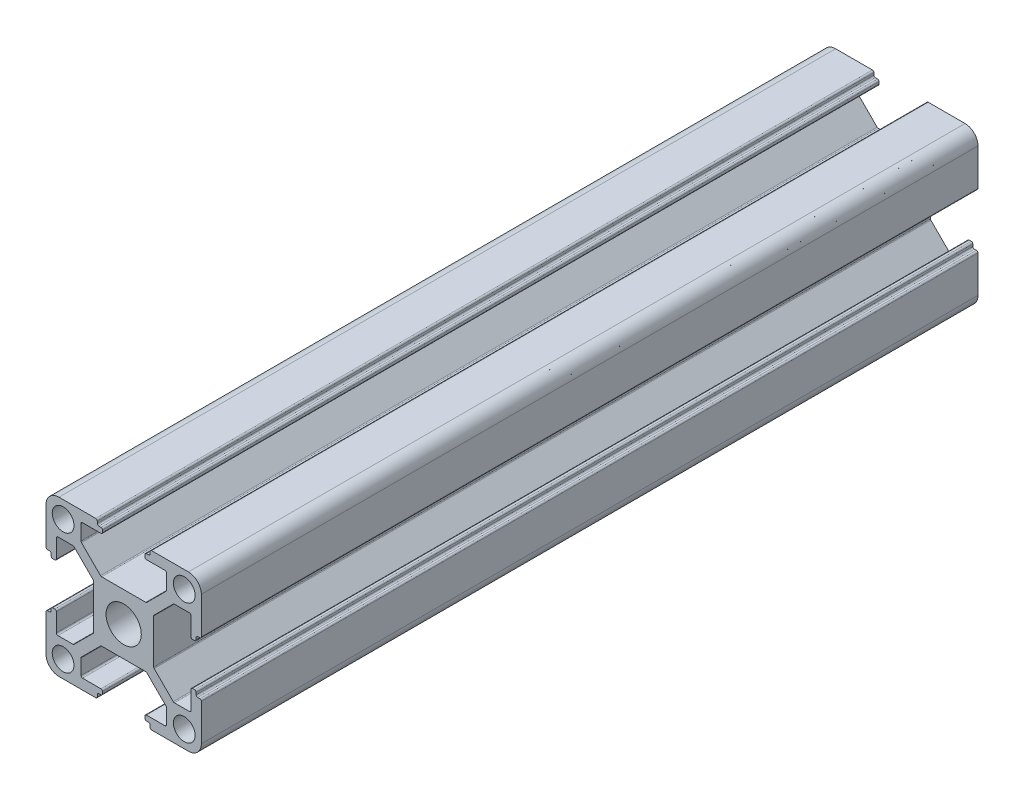
SolidWorks part; units mm, degrees
ref_plane "Alzado" through (0, 0, 0) normal (0, 0, 1) x (1, 0, 0)
ref_plane "Planta" through (0, 0, 0) normal (0, 1, 0) x (1, 0, 0)
ref_plane "Vista lateral" through (0, 0, 0) normal (1, 0, 0) x (0, 0, -1)
ref_plane "Plano1" through (0, 0, -50) normal (0, 0, -1) x (-1, 0, 0)
sketch "Croquis1" plane through (0, 0, -50) normal (0, 0, -1) x (-1, 0, 0)
  line L0 (14.7, -5.1) -> (14.3, -5.1)
  line L1 (14, -4.8) -> (14, -4.4)
  line L2 (13.7, -4.1) -> (13.3, -4.1)
  line L3 (13, -4.4) -> (13, -7.95)
  line L4 (12.7, -8.25) -> (9.7893, -8.25)
  line L5 (9.5772, -8.1622) -> (5.8879, -4.4739)
  line L6 (5.8, -4.2617) -> (5.8, 4.2607)
  line L7 (5.8879, 4.4729) -> (9.5771, 8.1621)
  line L8 (9.7893, 8.25) -> (12.7, 8.25)
  line L9 (13, 7.95) -> (13, 4.4)
  line L10 (13.3, 4.1) -> (13.7, 4.1)
  line L11 (14, 4.4) -> (14, 4.8)
  line L12 (14.3, 5.1) -> (14.7, 5.1)
  line L13 (15, 5.4) -> (15, 12.5)
  line L14 (12.5, 15) -> (5.4, 15)
  line L15 (5.1, 14.7) -> (5.1, 14.3)
  line L16 (4.8, 14) -> (4.4, 14)
  line L17 (4.1, 13.7) -> (4.1, 13.3)
  line L18 (4.4, 13) -> (7.95, 13)
  line L19 (8.25, 12.7) -> (8.25, 9.7883)
  line L20 (8.1621, 9.5761) -> (4.4739, 5.8879)
  line L21 (4.2617, 5.8) -> (-4.2607, 5.8)
  line L22 (-4.4728, 5.8878) -> (-8.1621, 9.5761)
  line L23 (-8.25, 9.7883) -> (-8.25, 12.7)
  line L24 (-7.95, 13) -> (-4.4, 13)
  line L25 (-4.1, 13.3) -> (-4.1, 13.7)
  line L26 (-4.4, 14) -> (-4.8, 14)
  line L27 (-5.1, 14.3) -> (-5.1, 14.7)
  line L28 (-5.4, 15) -> (-12.5, 15)
  line L29 (-15, 12.5) -> (-15, 5.4)
  line L30 (-14.7, 5.1) -> (-14.3, 5.1)
  line L31 (-14, 4.8) -> (-14, 4.4)
  line L32 (-13.7, 4.1) -> (-13.3, 4.1)
  line L33 (-13, 4.4) -> (-13, 7.95)
  line L34 (-12.7, 8.25) -> (-9.7883, 8.25)
  line L35 (-9.5761, 8.1621) -> (-5.8878, 4.4728)
  line L36 (-5.8, 4.2607) -> (-5.8, -4.2617)
  line L37 (-5.8879, -4.4739) -> (-9.5761, -8.1621)
  line L38 (-9.7883, -8.25) -> (-12.7, -8.25)
  line L39 (-13, -7.95) -> (-13, -4.4)
  line L40 (-13.3, -4.1) -> (-13.7, -4.1)
  line L41 (-14, -4.4) -> (-14, -4.8)
  line L42 (-14.3, -5.1) -> (-14.7, -5.1)
  line L43 (-15, -5.4) -> (-15, -12.5)
  line L44 (-12.5, -15) -> (-5.4, -15)
  line L45 (-5.1, -14.7) -> (-5.1, -14.3)
  line L46 (-4.8, -14) -> (-4.4, -14)
  line L47 (-4.1, -13.7) -> (-4.1, -13.3)
  line L48 (-4.4, -13) -> (-7.95, -13)
  line L49 (-8.25, -12.7) -> (-8.25, -9.7893)
  line L50 (-8.1621, -9.5771) -> (-4.4729, -5.8879)
  line L51 (-4.2607, -5.8) -> (4.2617, -5.8)
  line L52 (4.4739, -5.8879) -> (8.1622, -9.5772)
  line L53 (8.25, -9.7893) -> (8.25, -12.7)
  line L54 (7.95, -13) -> (4.4, -13)
  line L55 (4.1, -13.3) -> (4.1, -13.7)
  line L56 (4.4, -14) -> (4.8, -14)
  line L57 (5.1, -14.3) -> (5.1, -14.7)
  line L58 (5.4, -15) -> (12.5, -15)
  line L59 (15, -12.5) -> (15, -5.4)
  arc A0 (15, -5.4) -> (14.7, -5.1) centre (14.7, -5.4) ccw
  arc A1 (14.3, -5.1) -> (14, -4.8) centre (14.3, -4.8) cw
  arc A2 (14, -4.4) -> (13.7, -4.1) centre (13.7, -4.4) ccw
  arc A3 (13.3, -4.1) -> (13, -4.4) centre (13.3, -4.4) ccw
  arc A4 (13, -7.95) -> (12.7, -8.25) centre (12.7, -7.95) cw
  arc A5 (9.7893, -8.25) -> (9.5772, -8.1622) centre (9.7893, -7.95) cw
  arc A6 (5.8879, -4.4739) -> (5.8, -4.2617) centre (6.1, -4.2617) cw
  arc A7 (5.8, 4.2607) -> (5.8879, 4.4729) centre (6.1, 4.2607) cw
  arc A8 (9.5771, 8.1621) -> (9.7893, 8.25) centre (9.7893, 7.95) cw
  arc A9 (12.7, 8.25) -> (13, 7.95) centre (12.7, 7.95) cw
  arc A10 (13, 4.4) -> (13.3, 4.1) centre (13.3, 4.4) ccw
  arc A11 (13.7, 4.1) -> (14, 4.4) centre (13.7, 4.4) ccw
  arc A12 (14, 4.8) -> (14.3, 5.1) centre (14.3, 4.8) cw
  arc A13 (14.7, 5.1) -> (15, 5.4) centre (14.7, 5.4) ccw
  arc A14 (15, 12.5) -> (12.5, 15) centre (12.5, 12.5) ccw
  arc A15 (5.4, 15) -> (5.1, 14.7) centre (5.4, 14.7) ccw
  arc A16 (5.1, 14.3) -> (4.8, 14) centre (4.8, 14.3) cw
  arc A17 (4.4, 14) -> (4.1, 13.7) centre (4.4, 13.7) ccw
  arc A18 (4.1, 13.3) -> (4.4, 13) centre (4.4, 13.3) ccw
  arc A19 (7.95, 13) -> (8.25, 12.7) centre (7.95, 12.7) cw
  arc A20 (8.25, 9.7883) -> (8.1621, 9.5761) centre (7.95, 9.7883) cw
  arc A21 (4.4739, 5.8879) -> (4.2617, 5.8) centre (4.2617, 6.1) cw
  arc A22 (-4.2607, 5.8) -> (-4.4728, 5.8878) centre (-4.2607, 6.1) cw
  arc A23 (-8.1621, 9.5761) -> (-8.25, 9.7883) centre (-7.95, 9.7883) cw
  arc A24 (-8.25, 12.7) -> (-7.95, 13) centre (-7.95, 12.7) cw
  arc A25 (-4.4, 13) -> (-4.1, 13.3) centre (-4.4, 13.3) ccw
  arc A26 (-4.1, 13.7) -> (-4.4, 14) centre (-4.4, 13.7) ccw
  arc A27 (-4.8, 14) -> (-5.1, 14.3) centre (-4.8, 14.3) cw
  arc A28 (-5.1, 14.7) -> (-5.4, 15) centre (-5.4, 14.7) ccw
  arc A29 (-12.5, 15) -> (-15, 12.5) centre (-12.5, 12.5) ccw
  arc A30 (-15, 5.4) -> (-14.7, 5.1) centre (-14.7, 5.4) ccw
  arc A31 (-14.3, 5.1) -> (-14, 4.8) centre (-14.3, 4.8) cw
  arc A32 (-14, 4.4) -> (-13.7, 4.1) centre (-13.7, 4.4) ccw
  arc A33 (-13.3, 4.1) -> (-13, 4.4) centre (-13.3, 4.4) ccw
  arc A34 (-13, 7.95) -> (-12.7, 8.25) centre (-12.7, 7.95) cw
  arc A35 (-9.7883, 8.25) -> (-9.5761, 8.1621) centre (-9.7883, 7.95) cw
  arc A36 (-5.8878, 4.4728) -> (-5.8, 4.2607) centre (-6.1, 4.2607) cw
  arc A37 (-5.8, -4.2617) -> (-5.8879, -4.4739) centre (-6.1, -4.2617) cw
  arc A38 (-9.5761, -8.1621) -> (-9.7883, -8.25) centre (-9.7883, -7.95) cw
  arc A39 (-12.7, -8.25) -> (-13, -7.95) centre (-12.7, -7.95) cw
  arc A40 (-13, -4.4) -> (-13.3, -4.1) centre (-13.3, -4.4) ccw
  arc A41 (-13.7, -4.1) -> (-14, -4.4) centre (-13.7, -4.4) ccw
  arc A42 (-14, -4.8) -> (-14.3, -5.1) centre (-14.3, -4.8) cw
  arc A43 (-14.7, -5.1) -> (-15, -5.4) centre (-14.7, -5.4) ccw
  arc A44 (-15, -12.5) -> (-12.5, -15) centre (-12.5, -12.5) ccw
  arc A45 (-5.4, -15) -> (-5.1, -14.7) centre (-5.4, -14.7) ccw
  arc A46 (-5.1, -14.3) -> (-4.8, -14) centre (-4.8, -14.3) cw
  arc A47 (-4.4, -14) -> (-4.1, -13.7) centre (-4.4, -13.7) ccw
  arc A48 (-4.1, -13.3) -> (-4.4, -13) centre (-4.4, -13.3) ccw
  arc A49 (-7.95, -13) -> (-8.25, -12.7) centre (-7.95, -12.7) cw
  arc A50 (-8.25, -9.7893) -> (-8.1621, -9.5771) centre (-7.95, -9.7893) cw
  arc A51 (-4.4729, -5.8879) -> (-4.2607, -5.8) centre (-4.2607, -6.1) cw
  arc A52 (4.2617, -5.8) -> (4.4739, -5.8879) centre (4.2617, -6.1) cw
  arc A53 (8.1622, -9.5772) -> (8.25, -9.7893) centre (7.95, -9.7893) cw
  arc A54 (8.25, -12.7) -> (7.95, -13) centre (7.95, -12.7) cw
  arc A55 (4.4, -13) -> (4.1, -13.3) centre (4.4, -13.3) ccw
  arc A56 (4.1, -13.7) -> (4.4, -14) centre (4.4, -13.7) ccw
  arc A57 (4.8, -14) -> (5.1, -14.3) centre (4.8, -14.3) cw
  arc A58 (5.1, -14.7) -> (5.4, -15) centre (5.4, -14.7) ccw
  arc A59 (12.5, -15) -> (15, -12.5) centre (12.5, -12.5) ccw
  circle A60 centre (-11.7, 11.7) radius 2.1
  circle A61 centre (-11.7, -11.7) radius 2.1
  circle A62 centre (0, 0) radius 3.4
  circle A63 centre (11.7, 11.7) radius 2.1
  circle A64 centre (11.7, -11.7) radius 2.1
extrude "Saliente-Extruir1" add sketch "Croquis1" against normal blind 400
sketch "Croquis2" plane through (0, 0, -50) normal (0, 0, -1) x (-1, 0, 0)
  line L1 (-18.9895, 16.3918) -> (20.3186, 16.3918)
  line L2 (-18.9895, 16.3918) -> (-18.9895, -15.8279)
  line L3 (-18.9895, -15.8279) -> (20.3186, -15.8279)
  line L4 (20.3186, 16.3918) -> (20.3186, -15.8279)
extrude "Cortar-Extruir1" cut sketch "Croquis2" against normal blind 250
